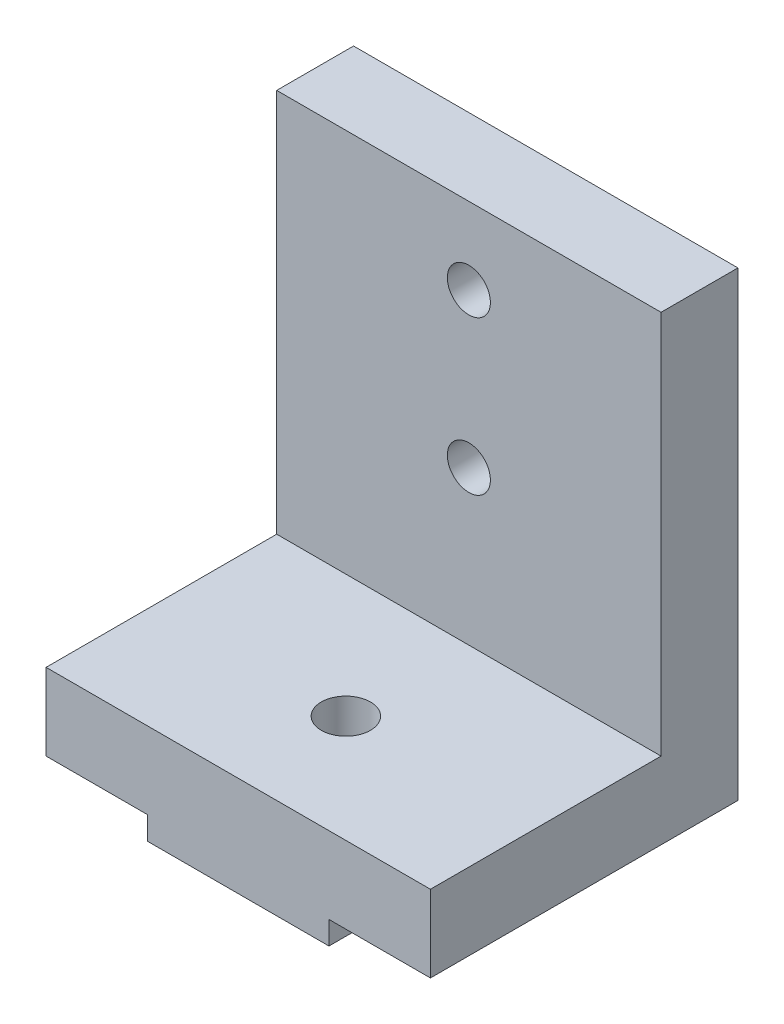
SolidWorks part; units mm, degrees
ref_plane "Front Plane" through (0, 0, 0) normal (0, 0, 1) x (1, 0, 0)
ref_plane "Top Plane" through (0, 0, 0) normal (0, 1, 0) x (1, 0, 0)
ref_plane "Right Plane" through (0, 0, 0) normal (1, 0, 0) x (0, 0, -1)
sketch "Sketch1" plane through (0, 0, 0) normal (0, 0, 1) x (1, 0, 0)
  line L1 (0, 0) -> (11.8, 0)
  line L2 (0, 0) -> (0, 1.5)
  line L3 (0, 1.5) -> (11.8, 1.5)
  line L4 (11.8, 0) -> (11.8, 1.5)
  line L5 (-6.6, 6.5) -> (18.4, 6.5)
  line L6 (-6.6, 6.5) -> (-6.6, 1.5)
  line L7 (-6.6, 1.5) -> (18.4, 1.5)
  line L8 (18.4, 6.5) -> (18.4, 1.5)
  dimension "D1" = 11.8
  dimension "D2" = 1.5
  dimension "D3" = 25
  dimension "D4" = 6.6
  dimension "D5" = 5
  dimension "D6" = 0
extrude "Boss-Extrude1" add sketch "Sketch1" along normal blind 20 contours L8 L5 L6 L7 L3 | L1 L4 L3 L2
sketch "Sketch3" plane through (0, 0, 0) normal (0, 0, -1) x (-1, 0, 0)
  line L1 (-18.4, 6.5) -> (6.6, 6.5)
  line L2 (-18.4, 6.5) -> (-18.4, 31.5)
  line L3 (-18.4, 31.5) -> (6.6, 31.5)
  line L4 (6.6, 6.5) -> (6.6, 31.5)
  circle A0 centre (-5.9, 16.5) radius 1.4
  circle A1 centre (-5.9, 26.5) radius 1.4
  dimension "D1" = 10
  dimension "D2" = 5
  dimension "D4" = 2.8
  dimension "D5" = 2.8
  dimension "D6" = 12.5
  dimension "D7" = 12.5
  dimension "D3" = 25
extrude "Boss-Extrude2" add sketch "Sketch3" against normal blind 5
sketch "Sketch4" plane through (0, 6.5, 0) normal (0, 1, 0) x (1, 0, 0)
  line L0 (-6.6, -20) -> (-6.6, -5) construction
  line L1 (-6.6, -20) -> (18.4, -20) construction
  circle A0 centre (5.9, -13) radius 1.6
  dimension "D1" = 12.5
  dimension "D2" = 3.2
  dimension "D3" = 7
extrude "Cut-Extrude2" cut sketch "Sketch4" against normal through all
